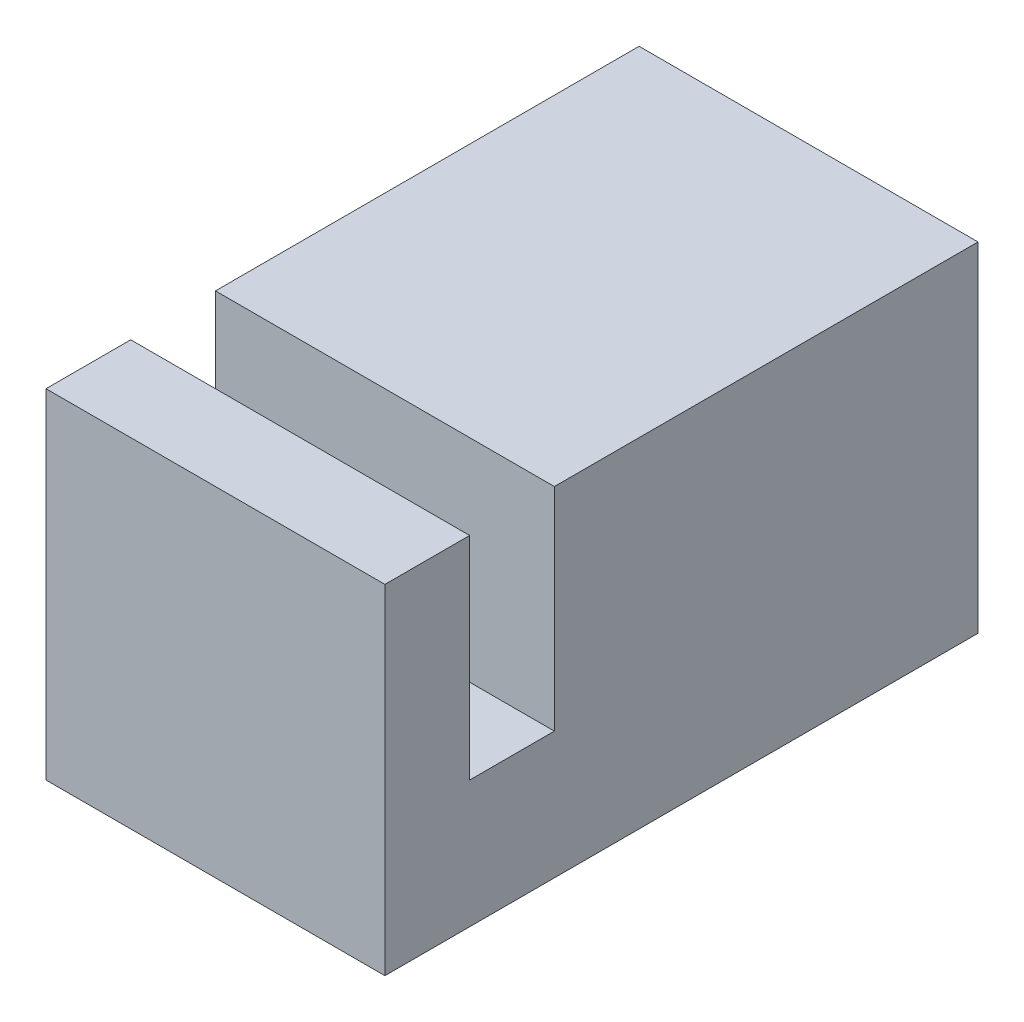
SolidWorks part; units mm, degrees
ref_plane "Płaszczyzna przednia" through (0, 0, 0) normal (0, 0, 1) x (1, 0, 0)
ref_plane "Płaszczyzna górna" through (0, 0, 0) normal (0, 1, 0) x (1, 0, 0)
ref_plane "Płaszczyzna prawa" through (0, 0, 0) normal (1, 0, 0) x (0, 0, -1)
sketch "Szkic1" plane through (0, 0, 0) normal (0, 0, 1) x (1, 0, 0)
  line L1 (0, 0) -> (8, 0)
  line L2 (0, 0) -> (0, 8)
  line L3 (0, 8) -> (8, 8)
  line L4 (8, 0) -> (8, 8)
  dimension "D1" = 8
  dimension "D2" = 8
extrude "Dodanie-wyciągnięcie1" add sketch "Szkic1" along normal blind 14
sketch "Szkic2" plane through (0, 8, 0) normal (0, 1, 0) x (1, 0, 0)
  line L0 (0, -14) -> (0, 0) construction
  line L1 (0, -10) -> (5, -10)
  line L2 (0, -10) -> (0, -12)
  line L3 (0, -12) -> (5, -12)
  line L5 (5, -10) -> (8, -10)
  line L6 (8, 0) -> (0, 0) construction
  line L8 (8, -14) -> (8, 0) construction
  line L9 (8, -10) -> (8, -12)
  line L10 (8, -12) -> (5, -12)
  dimension "D1" = 10
  dimension "D2" = 2
extrude "Wytnij-wyciągnięcie1" cut sketch "Szkic2" against normal blind 5
sketch "Szkic3" plane through (0, 0, 0) normal (0, 0, -1) x (-1, 0, 0)
  line L0 (0, 0) -> (-8, 0) construction
  line L1 (-8, 0) -> (-8, 8) construction
  circle A0 centre (-4, 4) radius 1.375
  dimension "D3" = 2.75
  dimension "D1" = 4
  dimension "D2" = 4
extrude "Wytnij-wyciągnięcie2" cut sketch "Szkic3" against normal blind 9
